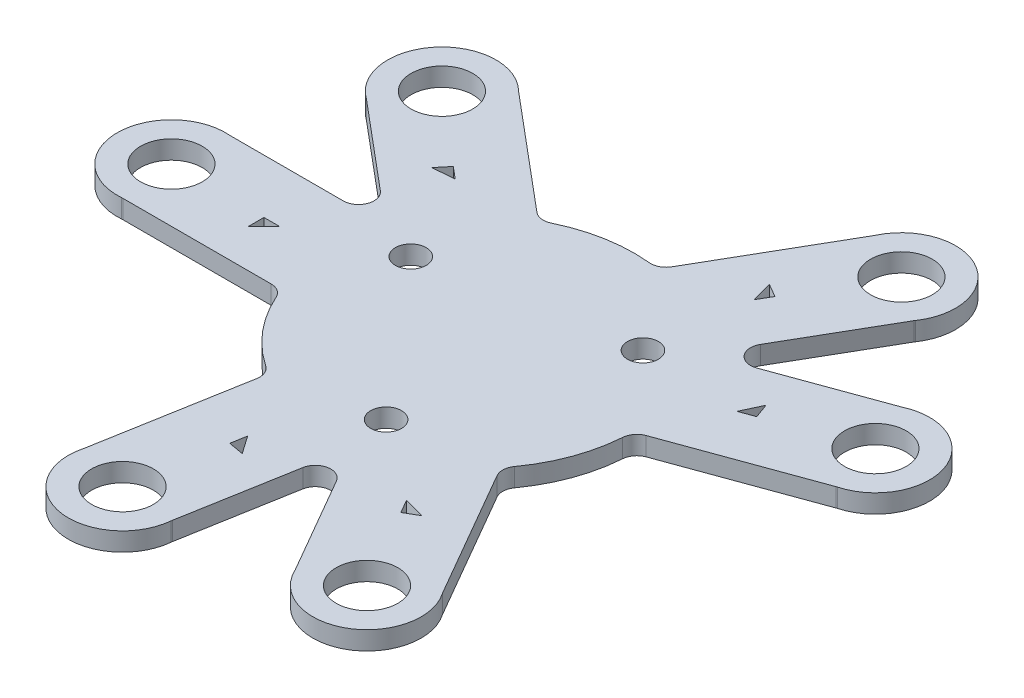
SolidWorks part; units mm, degrees
ref_plane "Front Plane" through (0, 0, 0) normal (0, 0, 1) x (1, 0, 0)
ref_plane "Top Plane" through (0, 0, 0) normal (0, 1, 0) x (1, 0, 0)
ref_plane "Right Plane" through (0, 0, 0) normal (1, 0, 0) x (0, 0, -1)
sketch "Sketch1" plane through (0, 0, 0) normal (0, 1, 0) x (1, 0, 0)
  line L0 (0, 0) -> (-20, 0) construction
  line L1 (0, 0) -> (10, 17.3205) construction
  line L2 (0, 0) -> (10, -17.3205) construction
  line L3 (0, 0) -> (-15.3209, 12.8558) construction
  line L4 (-19.6914, -3.5) -> (-9.3675, -3.5)
  line L5 (0, 0) -> (-3.473, -19.6962) construction
  line L6 (-17.15, 1.6) -> (-10.85, 1.6) construction
  line L7 (0, 0) -> (18.7939, 6.8404) construction
  line L8 (-17.15, 1.6) -> (-17.15, -1.6) construction
  line L9 (-17.15, -1.6) -> (-10.85, -1.6) construction
  line L10 (-10.85, 1.6) -> (-10.85, -1.6) construction
  line L11 (-17.15, 1.6) -> (-10.85, -1.6) construction
  line L12 (-17.15, -1.6) -> (-10.85, 1.6) construction
  line L13 (-19.6914, 3.5) -> (-9.3675, 3.5)
  line L14 (-17.3342, 9.9762) -> (-9.4257, 3.3402)
  line L15 (-12.8347, 15.3385) -> (-4.9262, 8.7025)
  line L16 (1.6527, 9.8625) -> (6.8146, 18.8032)
  line L17 (7.7148, 6.3625) -> (12.8768, 15.3032)
  line L18 (7.6055, 6.4928) -> (17.3068, 10.0238)
  line L19 (9.9996, -0.0851) -> (19.7009, 3.4459)
  line L20 (-5.0735, -8.6174) -> (-6.8662, -18.7844)
  line L21 (0.0275, -20) -> (1.8202, -9.833)
  line L22 (6.8146, -18.8032) -> (1.6527, -9.8625)
  line L23 (12.8768, -15.3032) -> (7.7148, -6.3625)
  line L24 (0, 0) -> (-9.6162, 3.5) construction
  line L25 (1.777, -10.0778) -> (0, 0) construction
  line L26 (7.8392, 6.5778) -> (0, 0) construction
  line L27 (-10.7246, 8.999) -> (-9.9586, 8.3562)
  line L28 (-14, 0) -> (-13, 0)
  line L29 (-14, 0) -> (-14, -1)
  line L32 (-10.7246, 8.999) -> (-11.3674, 8.233)
  line L35 (7, 12.1244) -> (6.5, 11.2583)
  line L36 (7, 12.1244) -> (6.134, 12.6244)
  line L39 (13.1557, 4.7883) -> (12.216, 4.4463)
  line L40 (13.1557, 4.7883) -> (12.8137, 5.728)
  line L43 (-2.2574, -12.8025) -> (-2.4311, -13.7873)
  line L45 (-2.4311, -13.7873) -> (-1.4463, -13.961)
  line L47 (7, -12.1244) -> (6.5, -11.2583)
  line L48 (7, -12.1244) -> (7.866, -11.6244)
  line L51 (-14, -1) -> (-13, 0)
  line L52 (-11.3674, 8.233) -> (-9.9586, 8.3562)
  line L53 (6.134, 12.6244) -> (6.5, 11.2583)
  line L54 (12.216, 4.4463) -> (12.8137, 5.728)
  line L55 (-2.2574, -12.8025) -> (-1.4463, -13.961)
  line L56 (6.5, -11.2583) -> (7.866, -11.6244)
  circle A0 centre (0, 0) radius 20 construction
  circle A1 centre (-20, 0) radius 2
  circle A2 centre (0, 0) radius 10
  arc A3 (-19.6914, 3.5) -> (-19.6914, -3.5) centre (-20, 0) ccw
  arc A4 (-12.8347, 15.3385) -> (-17.3342, 9.9762) centre (-15.3209, 12.8558) ccw
  arc A5 (12.8768, 15.3032) -> (6.8146, 18.8032) centre (10, 17.3205) ccw
  arc A6 (19.7009, 3.4459) -> (17.3068, 10.0238) centre (18.7939, 6.8404) ccw
  arc A7 (6.8146, -18.8032) -> (12.8768, -15.3032) centre (10, -17.3205) ccw
  arc A8 (-6.8662, -18.7844) -> (0.0275, -20) centre (-3.473, -19.6962) ccw
  circle A9 centre (-7.0477, 2.5652) radius 1
  circle A10 centre (0, 0) radius 7.5 construction
  circle A11 centre (5.7453, 4.8209) radius 1
  circle A12 centre (1.3024, -7.3861) radius 1
  circle A13 centre (-15.3209, 12.8558) radius 2
  circle A14 centre (10, 17.3205) radius 2
  circle A15 centre (18.7939, 6.8404) radius 2
  circle A16 centre (10, -17.3205) radius 2
  circle A17 centre (-3.473, -19.6962) radius 2
  point P9 (-14, 0)
  dimension "D9" = 20
  dimension "D11" = 4
  dimension "D12" = 2
  dimension "D13" = 15
  dimension "D1" = 120
  dimension "D2" = 120
  dimension "D5" = 20
  dimension "D3" = 40
  dimension "D4" = 40
  dimension "D6" = 40
  dimension "D7" = 6.3
  dimension "D8" = 3.2
  dimension "D10" = 7
  dimension "D14" = 6
  dimension "D15" = 1
  dimension "D16" = 6
  dimension "D17" = 6
  dimension "D18" = 6
  dimension "D19" = 6
  dimension "D20" = 6
extrude "Boss-Extrude1" add sketch "Sketch1" along normal blind 1.2 contours L13 A3 L4 A2 L14 L6 L10 L9 L8 A1 | A2 A12 A11 A9 | L20 A8 L21 L22 A2 A17 | L22 A7 L23 A2 L21 A16 | L19 A6 L18 L17 A2 A15 | L17 A5 L16 A2 L18 A14 | L15 A4 L14 L13 A2 A13 | A2 L13 L14 | A2 L22 L21 | A2 L17 L18 | L10 L6 L8 L9
fillet "Fillet1" radius 1 21 edges at (17.3068, 0.6, -10.0238) (19.7009, 0.6, -3.4459) (9.9996, 0.6, 0.0851) (7.7148, 0.6, 6.3625) (12.8768, 0.6, 15.3032) (6.8146, 0.6, 18.8032) (1.777, 0.6, 10.0778) (0.0275, 0.6, 20) (-6.8662, 0.6, 18.7844) (-5.0735, 0.6, 8.6174) (-19.6914, 0.6, 3.5) (-19.6914, 0.6, -3.5) (-9.6162, 0.6, -3.5) (-17.3342, 0.6, -9.9762) (-12.8347, 0.6, -15.3385) (-4.9262, 0.6, -8.7025) (1.6527, 0.6, -9.8625) (6.8146, 0.6, -18.8032) (12.8768, 0.6, -15.3032) (7.8392, 0.6, -6.5778) (-9.3675, 0.6, 3.5)
sketch "Sketch2" plane through (0, 1.2, 0) normal (0, 1, 0) x (1, 0, 0)
  line L0 (-3.4479, 7.0885) -> (6.504, -4.4535) construction
  line L1 (-6.1744, 4.7377) -> (3.7775, -6.8043)
  line L2 (-6.1744, 4.7377) -> (-0.7215, 9.4394)
  line L3 (-0.7215, 9.4394) -> (9.2304, -2.1026)
  line L4 (3.7775, -6.8043) -> (9.2304, -2.1026)
  line L5 (4.2545, 3.6684) -> (-1.1984, -1.0333) construction
  dimension "D1" = 15.24
  dimension "D2" = 7.2
equation "\"arm_angle\"= 40deg"
equation "\"table_radius\"= 20mm"
equation "\"table_height\"= 100mm"
equation "\"D5@Sketch1\"=\"table_radius\""
equation "\"D3@Sketch1\"=\"arm_angle\""
equation "\"D4@Sketch1\"=\"arm_angle\""
equation "\"D6@Sketch1\"=\"arm_angle\""
equation "\"arm_width\"= 7mm"
equation "\"D10@Sketch1\"=\"arm_width\""
